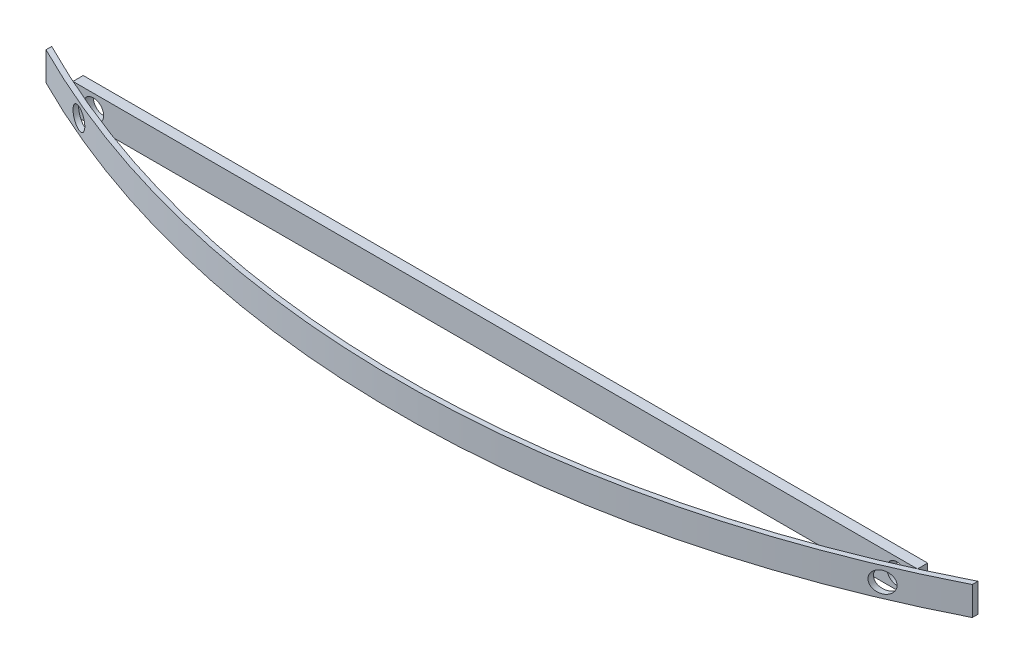
SolidWorks part; units mm, degrees
ref_plane "Front Plane" through (0, 0, 0) normal (0, 0, 1) x (1, 0, 0)
ref_plane "Top Plane" through (0, 0, 0) normal (0, 1, 0) x (1, 0, 0)
ref_plane "Right Plane" through (0, 0, 0) normal (1, 0, 0) x (0, 0, -1)
sketch "Sketch1" plane through (0, 0, 0) normal (0, 0, 1) x (1, 0, 0)
  line L0 (0, 0) -> (0, 140)
  line L1 (0, 140) -> (3930, 140)
  line L2 (3930, 140) -> (3930, 0)
  line L3 (3930, 0) -> (0, 0)
  dimension "D1" = 3930
  dimension "D2" = 140
extrude "Boss-Extrude1" add sketch "Sketch1" along normal blind 50
sketch "Sketch2" plane through (0, 0, 50) normal (0, 0, 1) x (1, 0, 0)
  line L0 (3930, 0) -> (3930, 140) construction
  line L1 (0, 140) -> (0, 0) construction
  circle A0 centre (3930, 70) radius 50
  circle A1 centre (0, 70) radius 50
  dimension "D1" = 100
  dimension "D2" = 100
extrude "Cut-Extrude1" cut sketch "Sketch2" against normal blind 50
sketch "Sketch3" plane through (0, 0, 0) normal (0, 0, -1) x (-1, 0, 0)
  line L0 (-3930, 140) -> (-4030, 140)
  line L1 (-4030, 140) -> (-4030, 0)
  line L2 (-4030, 0) -> (-3930, 0)
  line L3 (-3930, 0) -> (-3930, 140)
  line L4 (0, 140) -> (100, 140)
  line L5 (100, 140) -> (100, 0)
  line L6 (100, 0) -> (0, 0)
  line L7 (0, 0) -> (0, 140)
  dimension "D1" = 100
  dimension "D2" = 100
extrude "Boss-Extrude2" add sketch "Sketch3" against normal through all
sketch "Sketch4" plane through (0, 0, 0) normal (0, 0, -1) x (-1, 0, 0)
  line L0 (0, 120) -> (0, 20) construction
  line L1 (-3930, 20) -> (-3930, 120) construction
  circle A0 centre (0, 70) radius 50
  circle A1 centre (-3930, 70) radius 50
extrude "Cut-Extrude2" cut sketch "Sketch4" against normal through all
sketch "Sketch5" plane through (0, 0, 0) normal (0, -1, 0) x (1, 0, 0)
  line L0 (1965, 50) -> (1965, 929.1415) construction
  line L1 (-100, 50) -> (4030, 50) construction
  line L2 (-300, -46.1025) -> (-300, -18.0782)
  line L3 (4230, -46.1025) -> (4230, -18.0782)
  arc A0 (-100, 50) -> (4030, 50) centre (1965, -4503.6551) cw
  arc A1 (-100, 50) -> (-300, -46.1025) centre (1965, -4503.6551) ccw
  arc A2 (4030, 50) -> (4230, -46.1025) centre (1965, -4503.6551) cw
  arc A3 (-110.325, 72.7683) -> (-300, -18.0782) centre (1965, -4503.6551) ccw
  arc A4 (-110.325, 72.7683) -> (4040.325, 72.7683) centre (1965, -4503.6551) cw
  arc A5 (4040.325, 72.7683) -> (4230, -18.0782) centre (1965, -4503.6551) cw
  arc A6 (4040.325, 72.7683) -> (4241.325, -23.8148) centre (1965, -4503.6551) cw construction
  arc A7 (-110.325, 72.7683) -> (-311.325, -23.8148) centre (1965, -4503.6551) ccw construction
  dimension "D1" = 5000
  dimension "D3" = 25
  dimension "D2" = 200
extrude "Boss-Extrude3" add sketch "Sketch5" against normal through all separate body
sketch "Sketch6" plane through (0, 0, 0) normal (0, 0, -1) x (-1, 0, 0)
  circle A0 centre (-3930, 70) radius 50
  circle A1 centre (0, 70) radius 50
extrude "Cut-Extrude3" cut sketch "Sketch6" against normal through all
